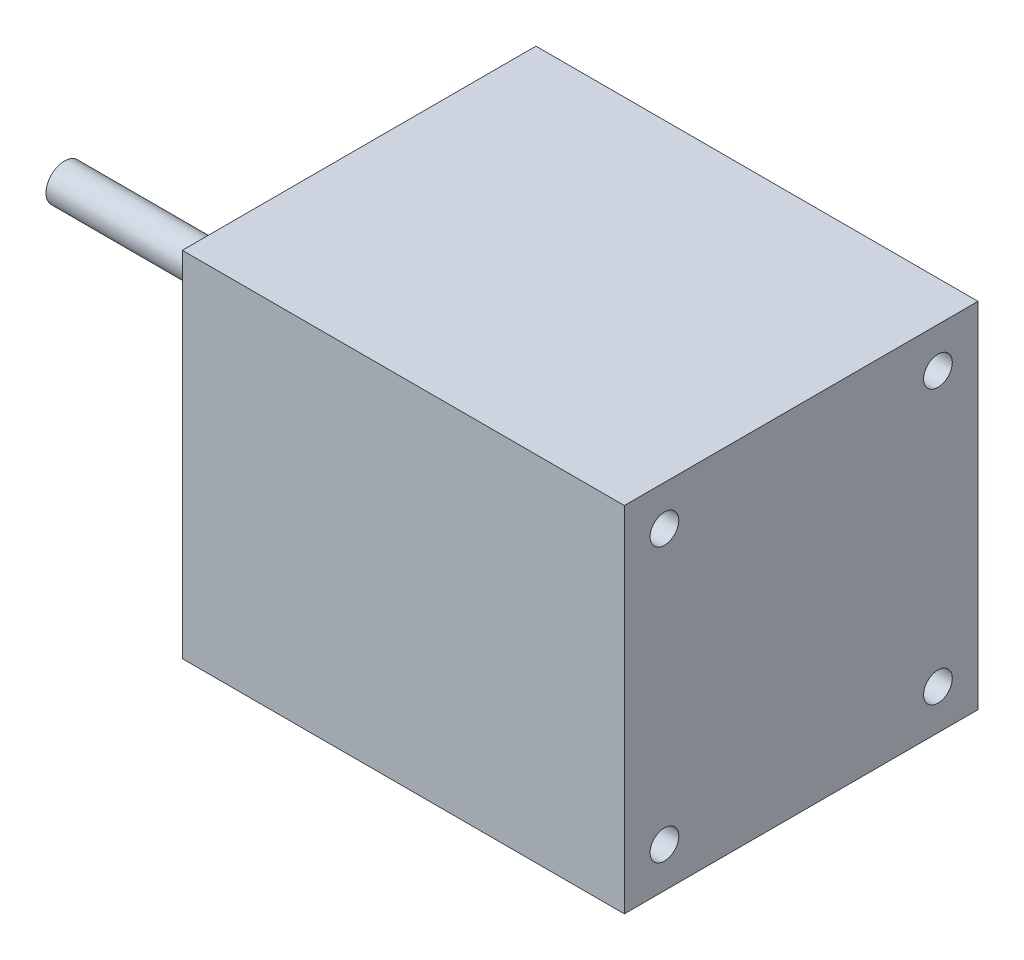
SolidWorks part; units mm, degrees
ref_plane "Front Plane" through (0, 0, 0) normal (0, 0, 1) x (1, 0, 0)
ref_plane "Top Plane" through (0, 0, 0) normal (0, 1, 0) x (1, 0, 0)
ref_plane "Right Plane" through (0, 0, 0) normal (1, 0, 0) x (0, 0, -1)
sketch "Sketch1" plane through (0, 0, 0) normal (1, 0, 0) x (0, 0, -1)
  line L1 (-30.48, -30.48) -> (30.48, -30.48)
  line L2 (-30.48, -30.48) -> (-30.48, 30.48)
  line L3 (-30.48, 30.48) -> (30.48, 30.48)
  line L4 (30.48, -30.48) -> (30.48, 30.48)
  line L5 (-30.48, -30.48) -> (30.48, 30.48) construction
  line L6 (-30.48, 30.48) -> (30.48, -30.48) construction
  circle A0 centre (0, 0) radius 33.3375 construction
  circle A1 centre (-23.5732, 23.5732) radius 2.4765
  circle A2 centre (23.5732, 23.5732) radius 2.4765
  circle A3 centre (23.5732, -23.5732) radius 2.4765
  circle A4 centre (-23.5732, -23.5732) radius 2.4765
  point P0 (0, 0)
  dimension "D3" = 66.675
  dimension "D4" = 4.953
  dimension "D5" = 4.953
  dimension "D6" = 4.953
  dimension "D7" = 4.953
  dimension "D1" = 60.96
  dimension "D2" = 60.96
extrude "Boss-Extrude3" add sketch "Sketch1" along normal blind 76.2 contours L4 L3 L2 L1 | A2 | A1 | A4 | A3
sketch "Sketch3" plane through (0, 0, 0) normal (-1, 0, 0) x (0, 0, 1)
  circle A0 centre (0, 0) radius 3.175
  dimension "D1" = 6.35
extrude "Boss-Extrude4" add sketch "Sketch3" along normal blind 50.8
